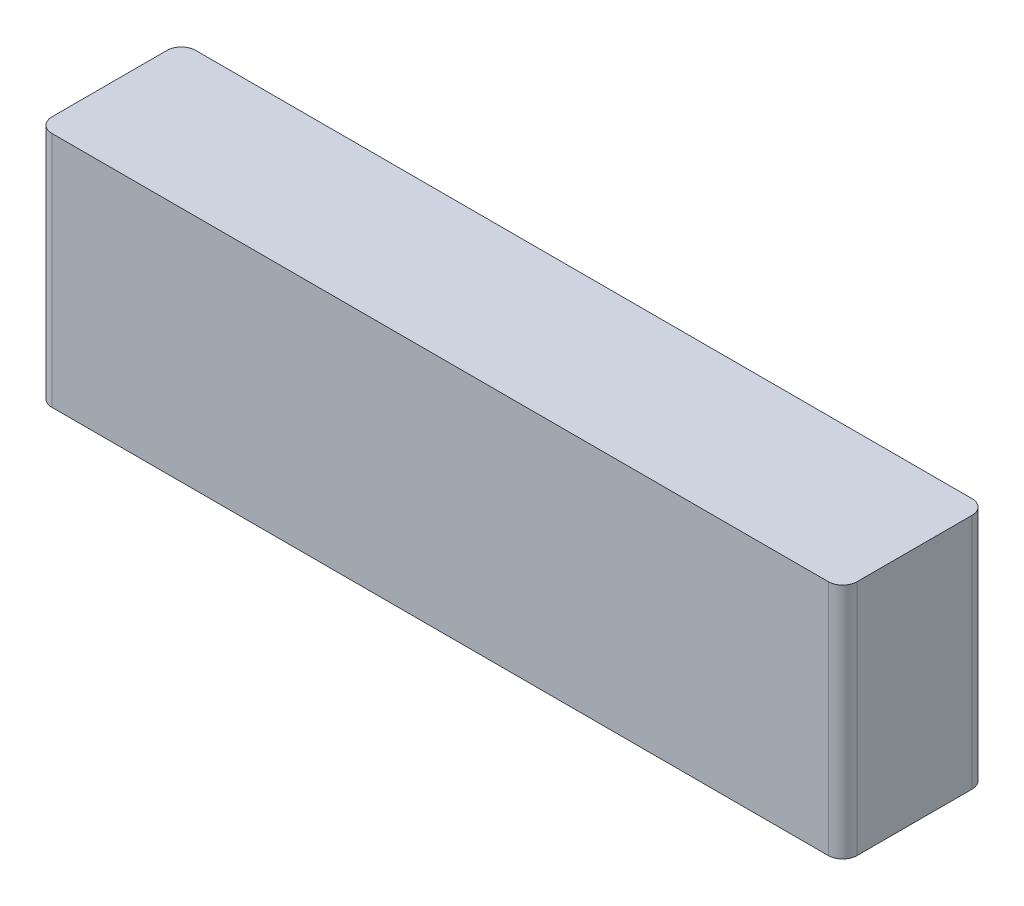
SolidWorks part; units mm, degrees
ref_plane "Front Plane" through (0, 0, 0) normal (0, 0, 1) x (1, 0, 0)
ref_plane "Top Plane" through (0, 0, 0) normal (0, 1, 0) x (1, 0, 0)
ref_plane "Right Plane" through (0, 0, 0) normal (1, 0, 0) x (0, 0, -1)
sketch "Sketch1" plane through (0, 0, 0) normal (0, 1, 0) x (1, 0, 0)
  line L1 (-56, -10) -> (56, -10)
  line L2 (-56, -10) -> (-56, 10)
  line L3 (-56, 10) -> (56, 10)
  line L4 (56, -10) -> (56, 10)
  line L5 (-56, -10) -> (56, 10) construction
  line L6 (-56, 10) -> (56, -10) construction
  point P0 (0, 0)
  dimension "D1" = 112
  dimension "D2" = 20
extrude "Boss-Extrude1" add sketch "Sketch1" along normal blind 33
fillet "Fillet1" radius 2 4 edges at (-56, 16.5, 10) (-56, 16.5, -10) (56, 16.5, -10) (56, 16.5, 10)
